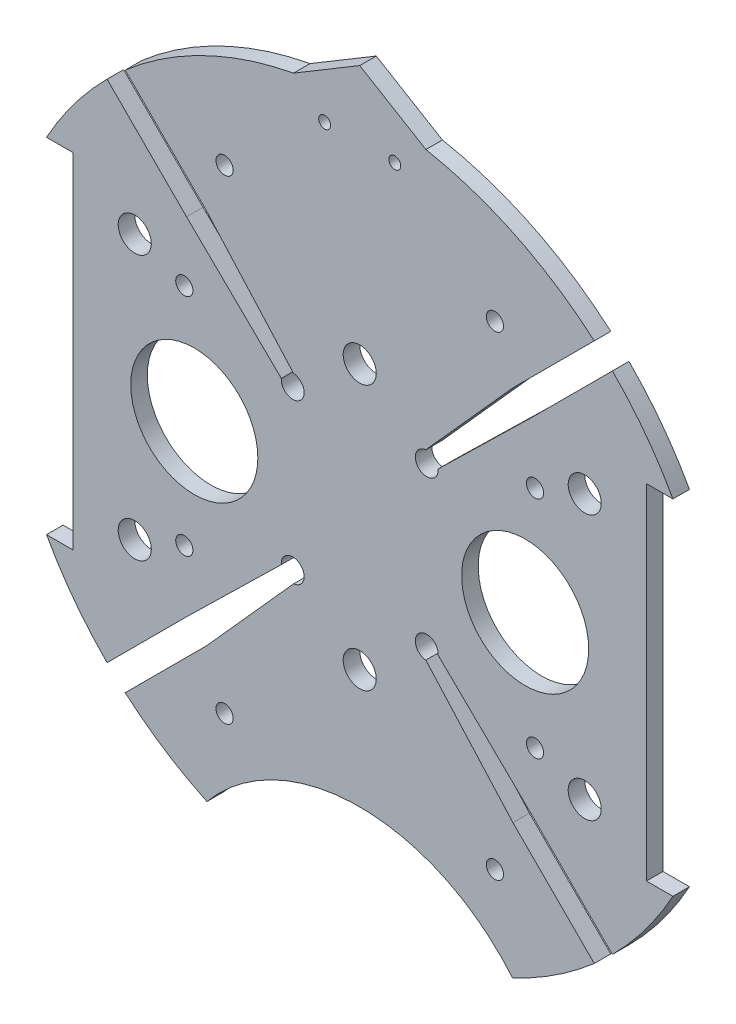
SolidWorks part; units mm, degrees
ref_plane "Front Plane" through (0, 0, 0) normal (0, 0, 1) x (1, 0, 0)
ref_plane "Top Plane" through (0, 0, 0) normal (0, 1, 0) x (1, 0, 0)
ref_plane "Right Plane" through (0, 0, 0) normal (1, 0, 0) x (0, 0, -1)
sketch "Sketch1" plane through (0, 0, 0) normal (0, 0, 1) x (1, 0, 0)
  line L0 (0, 0) -> (-82.1241, 0) construction
  line L1 (0, 0) -> (0, 95.6219) construction
  line L3 (-60.1074, 33.02) -> (-55.0274, 33.02)
  line L5 (-60.1074, -33.02) -> (-55.0274, -33.02)
  line L6 (-55.0274, 33.02) -> (-55.0274, -33.02)
  line L7 (60.1074, -33.02) -> (55.0274, -33.02)
  line L8 (60.1074, 33.02) -> (55.0274, 33.02)
  line L9 (55.0274, 33.02) -> (55.0274, -33.02)
  arc A0 (-60.1074, -33.02) -> (60.1074, -33.02) centre (0, 0) ccw
  circle A1 centre (-46.482, 10.795) radius 1.651 construction
  circle A2 centre (-21.082, 10.795) radius 1.651 construction
  circle A3 centre (-21.082, -10.795) radius 1.651 construction
  circle A4 centre (-46.482, -10.795) radius 1.651 construction
  circle A5 centre (46.482, -10.795) radius 1.651 construction
  circle A6 centre (21.082, -10.795) radius 1.651 construction
  circle A7 centre (21.082, 10.795) radius 1.651 construction
  circle A8 centre (46.482, 10.795) radius 1.651 construction
  arc A9 (60.1074, 33.02) -> (-60.1074, 33.02) centre (0, 0) ccw
  dimension "D2" = 3.302
  dimension "D3" = 3.302
  dimension "D4" = 25.4
  dimension "D5" = 10.795
  dimension "D10" = 46.482
  dimension "D12" = 10.795
  dimension "D6" = 66.04
  dimension "D7" = 5.08
  dimension "D8" = 68.58
  dimension "D9" = 68.58
  dimension "D11" = 33.02
extrude "Boss-Extrude2" add sketch "Sketch1" along normal blind 3.175
sketch "Sketch4" plane through (0, 0, 0) normal (0, 0, -1) x (-1, 0, 0)
  line L0 (0, 0) -> (0, -122.8047) construction
  line L1 (33.02, -67.2621) -> (-33.02, -67.2621)
  arc A0 (-60.1074, -33.02) -> (60.1074, -33.02) centre (0, 0) ccw construction
  circle A1 centre (0, -86.3121) radius 38.1
  dimension "D4" = 76.2
  dimension "D5" = 0
  dimension "D6" = 19.05
  dimension "D1" = 74.93
  dimension "D2" = 74.93
  dimension "D3" = 66.04
extrude "Cut-Extrude3" cut sketch "Sketch4" against normal through all
sketch "Sketch5" plane through (0, 0, 0) normal (0, 0, -1) x (-1, 0, 0)
  line L0 (45.1258, 51.861) -> (11.5228, 18.258) construction
  line L1 (-69.4248, 0) -> (69.4248, 0) construction
  line L2 (48.4934, -48.4934) -> (33.2448, -33.2448)
  line L3 (15.0507, 15.4792) -> (33.2448, 33.2448)
  line L4 (29.4103, -36.1455) -> (45.1258, -51.861)
  line L5 (45.1258, -51.861) -> (48.4934, -48.4934)
  line L6 (-15.2664, -15.2664) -> (-65.8076, -65.8076) construction
  line L7 (15.5824, -17.3784) -> (-2.7323, 0.9363) construction
  line L8 (12.6806, 17.4737) -> (29.4103, 36.1455)
  line L9 (-48.4934, 48.4934) -> (-6.6635, 6.6635) construction
  line L10 (-12.6806, 17.4737) -> (-29.4103, 36.1455)
  line L11 (48.4934, 48.4934) -> (15.2664, 15.2664) construction
  line L12 (-15.0507, 15.4792) -> (-33.2448, 33.2448)
  line L13 (0, 0) -> (46.9211, -12.5725) construction
  line L14 (29.4103, -36.1455) -> (12.6806, -17.4737)
  line L15 (-45.1258, 51.861) -> (-11.6404, 18.1832) construction
  line L16 (-45.1258, -51.861) -> (-13.0585, -19.7937) construction
  line L17 (45.1258, -51.861) -> (17.3018, -24.037) construction
  line L18 (0, 0) -> (-46.9211, -12.5725) construction
  line L19 (0, 0) -> (-0.898, -0.898) construction
  line L20 (33.2448, -33.2448) -> (15.0507, -15.4792)
  line L21 (4.9069, -1.3148) -> (-4.984, 8.5761) construction
  line L22 (-29.4103, -36.1455) -> (-12.6806, -17.4737)
  line L23 (-33.2448, -33.2448) -> (-15.0507, -15.4792)
  line L27 (-45.1258, -51.861) -> (-48.4934, -48.4934)
  line L28 (-29.4103, -36.1455) -> (-45.1258, -51.861)
  line L30 (0, 58.5122) -> (0, -56.1975) construction
  line L31 (-48.4934, -48.4934) -> (-33.2448, -33.2448)
  line L34 (-48.4934, 48.4934) -> (-33.2448, 33.2448)
  line L36 (-29.4103, 36.1455) -> (-45.1258, 51.861)
  line L37 (-45.1258, 51.861) -> (-48.4934, 48.4934)
  line L43 (15.2664, -15.2664) -> (65.8076, -65.8076) construction
  line L47 (0, 6.7352) -> (-14.4605, -7.7253) construction
  line L53 (45.1258, 51.861) -> (48.4934, 48.4934)
  line L54 (29.4103, 36.1455) -> (45.1258, 51.861)
  line L56 (48.4934, 48.4934) -> (33.2448, 33.2448)
  circle A0 centre (0, 0) radius 21.59 construction
  arc A1 (29.3285, -61.9924) -> (60.1074, -33.02) centre (0, 0) ccw construction
  arc A2 (12.6806, -17.4737) -> (15.0507, -15.4792) centre (12.8656, -15.2882) cw
  arc A3 (15.0507, 15.4792) -> (12.6806, 17.4737) centre (12.8656, 15.2882) cw
  arc A4 (-12.6806, 17.4737) -> (-15.0507, 15.4792) centre (-12.8656, 15.2882) cw
  arc A5 (-12.6806, -17.4737) -> (-15.0507, -15.4792) centre (-12.8656, -15.2882) ccw
  dimension "D6" = 43.18
  dimension "D2" = 4.7625
  dimension "D3" = 22.225
  dimension "D9" = 15
extrude "Cut-Extrude6" cut sketch "Sketch5" against normal through all
sketch "Sketch9" plane through (0, 0, 0) normal (0, 0, -1) x (-1, 0, 0)
  line L0 (12.7, 67.3938) -> (0, 75)
  line L1 (0, 75) -> (-12.7, 67.3938)
  arc A2 (12.7, 67.3938) -> (-12.7, 67.3938) centre (0, 0) ccw
extrude "Boss-Extrude3" add sketch "Sketch9" against normal blind 3.175
extrude "Cut-Extrude7" cut sketch "Sketch10" against normal through all
sketch "Sketch10" plane through (-31.3134, 132.559, 6.35) normal (0, 0, 1) x (0, 1, 0)
  line L0 (-132.559, -31.3134) -> (-245.9178, -31.3134) construction
  line L1 (-132.559, -31.3134) -> (-132.559, -129.4011) construction
  circle A0 centre (-180.819, -4.6434) radius 1.651
  circle A3 centre (-180.819, -57.9834) radius 1.651
  circle A4 centre (-84.299, -57.9834) radius 1.651
  circle A5 centre (-84.299, -4.6434) radius 1.651
extrude "Cut-Extrude8" cut sketch "Sketch11" against normal through all both and the other way through all
sketch "Sketch11" plane through (-31.3134, 132.614, 38.1) normal (0, 0, 1) x (0, 1, 0)
  line L0 (-132.614, -31.3134) -> (-132.614, 57.8454) construction
  line L1 (-132.614, -31.3134) -> (-222.516, -31.3134) construction
  circle A0 centre (-158.014, 14.4066) radius 3.175
  circle A1 centre (-173.254, -31.3134) radius 3.175
  circle A3 centre (-158.014, -77.0334) radius 3.175
  circle A4 centre (-107.214, -77.0334) radius 3.175
  circle A5 centre (-91.974, -31.3134) radius 3.175
  circle A6 centre (-107.214, 14.4066) radius 3.175
sketch "Sketch12" plane through (0, 0, 0) normal (0, 0, -1) x (-1, 0, 0)
  line L0 (0, -13.969) -> (0, 24.0636) construction
  circle A0 centre (6.731, 62.23) radius 1.143
  circle A1 centre (-6.731, 62.23) radius 1.143
  dimension "D1" = 2.286
  dimension "D2" = 62.23
  dimension "D3" = 6.731
extrude "Cut-Extrude9" cut sketch "Sketch12" against normal through all
extrude "Cut-Extrude11" cut sketch "Sketch14" against normal through all and the other way blind 103.378
sketch "Sketch14" plane through (30.092, 4.0835, 15.875) normal (0, 0, -1) x (-1, 0, 0)
  line L0 (30.092, -4.0835) -> (148.6336, -4.0835) construction
  line L1 (30.092, -4.0835) -> (30.092, 90.452) construction
  circle A0 centre (-13.088, 21.3165) radius 3.175
  circle A1 centre (73.272, 21.3165) radius 3.175
  circle A2 centre (30.092, 21.3165) radius 3.175
  circle A4 centre (73.272, -29.4835) radius 3.175
  circle A5 centre (30.092, -29.4835) radius 3.175
  circle A6 centre (-13.088, -29.4835) radius 3.175
extrude "Cut-Extrude12" cut sketch "Sketch15" against normal blind 75.692
sketch "Sketch15" plane through (30.092, 4.0835, -25.527) normal (0, 0, -1) x (-1, 0, 0)
  circle A0 centre (63.7572, 17.5065) radius 1.651
  circle A1 centre (63.7572, -25.6735) radius 1.651
  circle A2 centre (-3.5528, -25.6735) radius 1.651
  circle A3 centre (-3.5528, 17.5065) radius 1.651
extrude "Cut-Extrude14" cut sketch "Sketch17" against normal blind 97.79
sketch "Sketch17" plane through (30.092, 4.0835, -31.75) normal (0, 0, -1) x (-1, 0, 0)
  line L0 (30.092, -29.4835) -> (30.092, 6.2385) construction
  circle A0 centre (4.1544, -49.7288) radius 1.651
  circle A4 centre (56.0296, -49.7288) radius 1.651
  circle A5 centre (4.1544, 41.3825) radius 1.651
  circle A9 centre (56.0296, 41.3825) radius 1.651
sketch "Sketch18" plane through (0, 0, 0) normal (0, 0, -1) x (-1, 0, 0)
  line L0 (0, 0) -> (0, -37.9941) construction
  circle A0 centre (31.75, 0) radius 12.192
  circle A1 centre (-31.75, 0) radius 12.192
  dimension "D1" = 24.384
  dimension "D2" = 31.75
extrude "Cut-Extrude15" cut sketch "Sketch18" against normal blind 35.56
